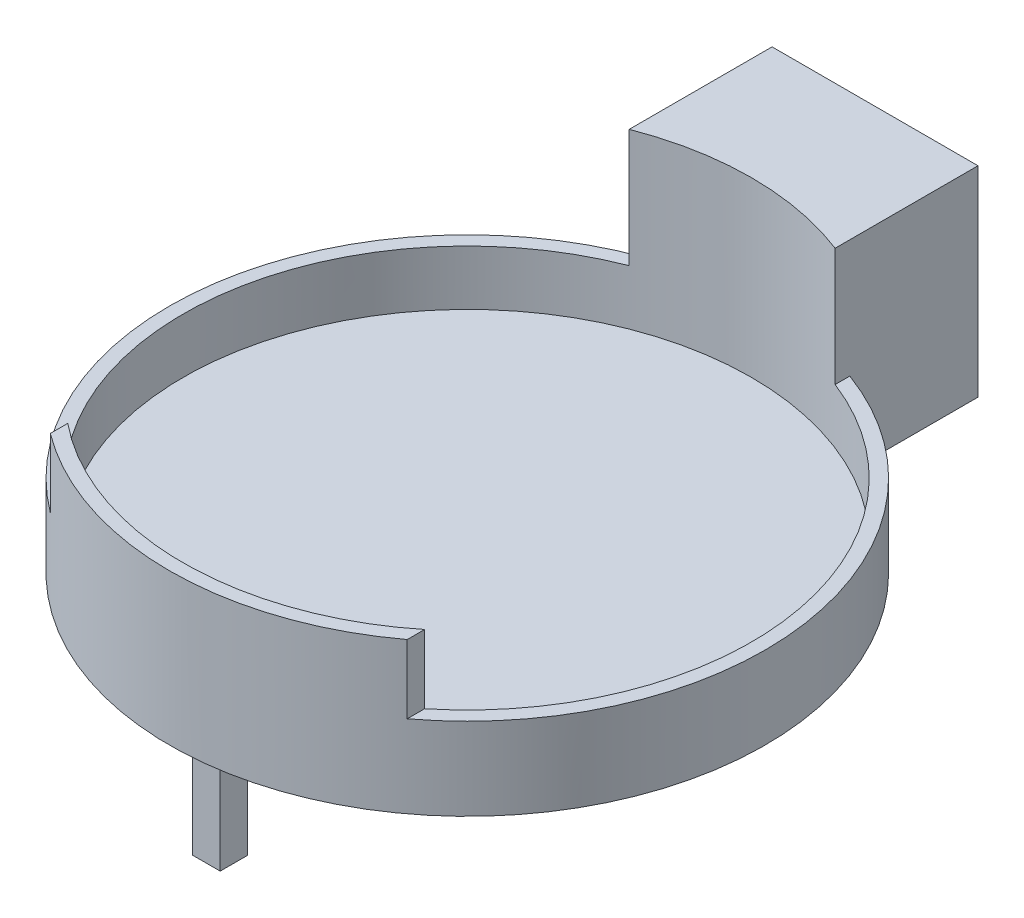
SolidWorks part; units mm, degrees
material "ABS"
ref_plane "Front Plane" through (0, 0, 0) normal (0, 0, 1) x (1, 0, 0)
ref_plane "Top Plane" through (0, 0, 0) normal (0, 1, 0) x (1, 0, 0)
ref_plane "Right Plane" through (0, 0, 0) normal (1, 0, 0) x (0, 0, -1)
sketch "Sketch1" plane through (0, 0, 0) normal (0, 1, 0) x (1, 0, 0)
  circle A0 centre (0, 0) radius 10.85
  dimension "D1" = 21.7
extrude "Boss-Extrude1" add sketch "Sketch1" along normal blind 1
sketch "Sketch2" plane through (0, 0, 0) normal (0, -1, 0) x (1, 0, 0)
  line L1 (0.5, 8.5) -> (-0.5, 8.5)
  line L2 (0.5, 8.5) -> (0.5, 9.5)
  line L3 (0.5, 9.5) -> (-0.5, 9.5)
  line L4 (-0.5, 8.5) -> (-0.5, 9.5)
  line L5 (0.5, 8.5) -> (-0.5, 9.5) construction
  line L6 (0.5, 9.5) -> (-0.5, 8.5) construction
  circle A0 centre (0, 0) radius 10.85 construction
  point P0 (0, 9)
  point P5 (-2.2685, 0)
  point P9 (-2.8, 10.4825)
  point P10 (0, 3.4089)
  point P11 (0, 0)
  dimension "D1" = 1
  dimension "D2" = 1
  dimension "D3" = 3.3
  dimension "D4" = 9
extrude "Boss-Extrude2" add sketch "Sketch2" along normal blind 4.4
pattern_circular "CirPattern1" count 2 over 360 about axis through (0, 0, 0) along (0, 1, 0) of "Boss-Extrude2"
sketch "Sketch3" plane through (0, 1, 0) normal (0, 1, 0) x (1, 0, 0)
  circle A0 centre (0, 0) radius 10.85
  circle A1 centre (0, 0) radius 10.35
  circle A2 centre (0, 0) radius 10.85 construction
  dimension "D1" = 0.5
extrude "Boss-Extrude3" add sketch "Sketch3" along normal blind 6.3
sketch "Sketch4" plane through (0, 7.3, 0) normal (0, 1, 0) x (1, 0, 0)
  line L0 (-3.75, 9.6468) -> (-3.75, 10.1814)
  line L1 (3.75, 9.6468) -> (3.75, 10.1814)
  line L2 (-3.75, 9.6468) -> (3.75, 9.6468) construction
  circle A0 centre (0, 0) radius 10.35 construction
  circle A1 centre (0, 0) radius 10.85
  arc A2 (-3.75, 10.1814) -> (3.75, 10.1814) centre (0, 0) ccw
  arc A3 (-3.75, 9.6468) -> (3.75, 9.6468) centre (0, 0) ccw
  circle A4 centre (0, 0) radius 10.85 construction
  dimension "D2" = 7.5
  dimension "D1" = 0
extrude "Cut-Extrude1" cut sketch "Sketch4" against normal offset from surface (1.8 mm away) 4.5 up to face at (0, 1, 10.35)
sketch "Sketch7" plane through (0, 5.5, 0) normal (0, 1, 0) x (1, 0, 0)
  line L0 (-6.5, -8.6875) -> (-6.5, -8.0543)
  line L1 (6.5, -8.6875) -> (6.5, -8.0543)
  line L2 (-3.75, 9.6468) -> (-3.75, 10.1814)
  line L3 (3.75, 10.1814) -> (3.75, 9.6468)
  line L4 (-3.75, 9.6468) -> (-3.75, 10.1814)
  line L5 (3.75, 10.1814) -> (3.75, 9.6468)
  line L6 (-6.5, -8.0543) -> (6.5, -8.0543) construction
  arc A0 (6.5, -8.0543) -> (3.75, 9.6468) centre (0, 0) ccw
  arc A1 (6.5, -8.6875) -> (3.75, 10.1814) centre (0, 0) ccw
  arc A2 (-3.75, 9.6468) -> (3.75, 9.6468) centre (0, 0) ccw
  arc A3 (-3.75, 10.1814) -> (3.75, 10.1814) centre (0, 0) ccw
  arc A4 (-3.75, 9.6468) -> (-6.5, -8.0543) centre (0, 0) ccw
  arc A5 (-3.75, 10.1814) -> (-6.5, -8.6875) centre (0, 0) ccw
  dimension "D2" = 13
  dimension "D1" = 0
extrude "Cut-Extrude4" cut sketch "Sketch7" against normal offset from surface 2 and the other way through all up to face at (0, 1, 10.35)
sketch "Sketch8" plane through (0, 0, 0) normal (0, -1, 0) x (1, 0, 0)
  line L0 (-3.75, -10.1814) -> (-3.75, -14.85)
  line L1 (-3.75, -14.85) -> (3.75, -14.85)
  line L2 (3.75, -14.85) -> (3.75, -10.1814)
  circle A0 centre (0, 0) radius 10.85 construction
  arc A1 (-3.75, -10.1814) -> (3.75, -10.1814) centre (0, 0) ccw
  point P4 (0, -10.85)
  dimension "D1" = 7.5
  dimension "D2" = 4
extrude "Boss-Extrude4" add sketch "Sketch8" against normal up to surface (7.3 mm away) up to face at (0, 7.3, -10.257)
